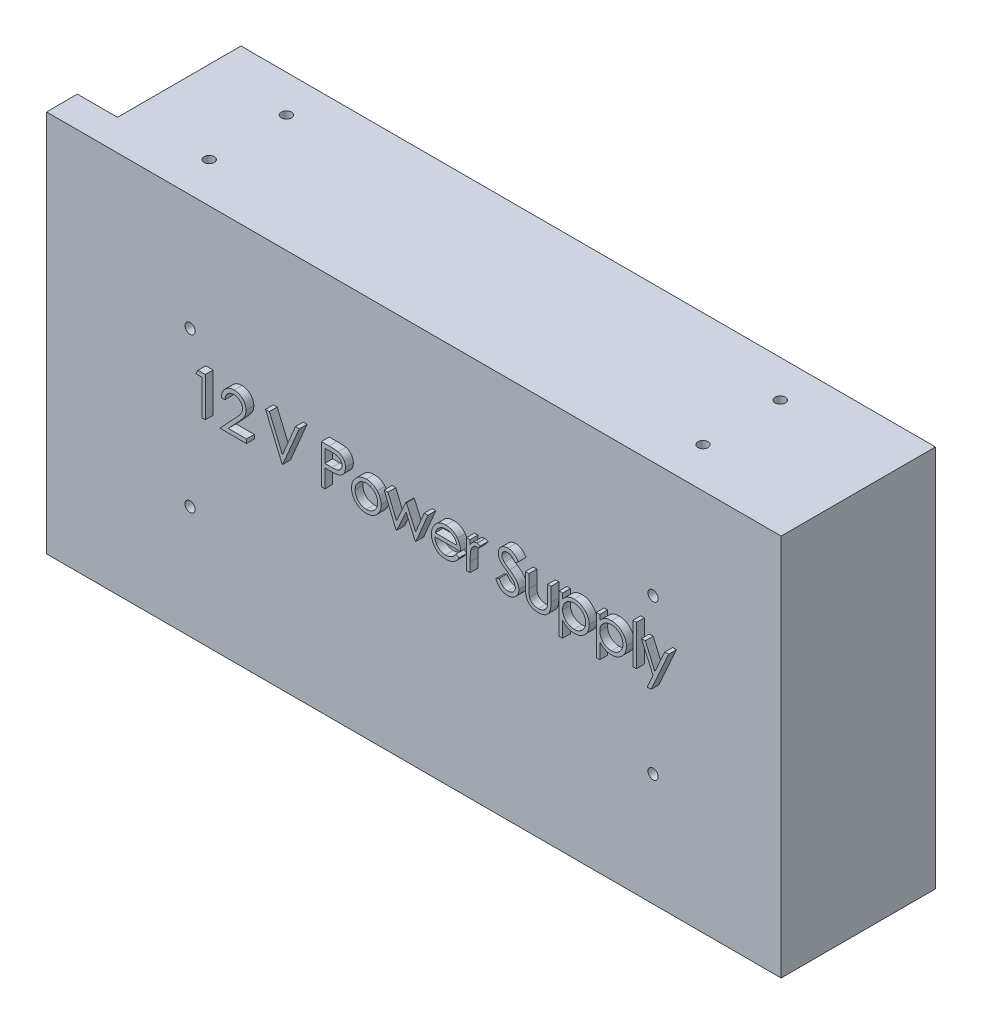
SolidWorks part; units mm, degrees
ref_plane "Front Plane" through (0, 0, 0) normal (0, 0, 1) x (1, 0, 0)
ref_plane "Top Plane" through (0, 0, 0) normal (0, 1, 0) x (1, 0, 0)
ref_plane "Right Plane" through (0, 0, 0) normal (1, 0, 0) x (0, 0, -1)
sketch "Sketch1" plane through (0, 0, 0) normal (0, 0, 1) x (1, 0, 0)
  line L1 (112.5, -62) -> (-112.5, -62)
  line L2 (112.5, -62) -> (112.5, 62)
  line L3 (112.5, 62) -> (-112.5, 62)
  line L4 (-112.5, -62) -> (-112.5, 62)
  line L5 (112.5, -62) -> (-112.5, 62) construction
  line L6 (112.5, 62) -> (-112.5, -62) construction
  point P0 (0, 0)
  dimension "D1" = 225
  dimension "D2" = 124
extrude "Boss-Extrude1" add sketch "Sketch1" along normal blind 50
sketch "Sketch2" plane through (0, 0, 50) normal (0, 0, 1) x (1, 0, 0)
  text T0 "12 V Power Supply" font "Century Gothic" height in points 48
extrude "Boss-Extrude2" add sketch "Sketch2" along normal blind 2.54
sketch "Sketch3" plane through (-112.5, 0, 0) normal (-1, 0, 0) x (0, 0, 1)
  line L0 (50, 62) -> (0, 62) construction
  line L1 (50, -62) -> (40, -62)
  line L2 (50, -62) -> (50, 62)
  line L3 (50, 62) -> (40, 62)
  line L4 (40, -62) -> (40, 62)
  dimension "D1" = 10
extrude "Boss-Extrude3" add sketch "Sketch3" along normal blind 13
hole_wizard "Tap Drill for M4x0.7 Tap1" positions "Sketch6" profile "Sketch7" hole size "M4x0.7" standard "ANSI Metric"
sketch "Sketch6" plane through (0, 0, 50) normal (0, 0, -1) x (-1, 0, 0)
  line L0 (-112.5, 62) -> (112.5, 62) construction
  line L2 (112.5, 62) -> (112.5, -62) construction
  point P0 (-71, 24.5)
  point P2 (79, 24.5)
  point P4 (79, -25.5)
  point P6 (-71, -25.5)
  dimension "D1" = 37.5
  dimension "D2" = 50
  dimension "D3" = 150
  dimension "D4" = 33.5
sketch "Sketch7" plane through (71, 24.5, 50) normal (1, 0, 0) x (0, -1, 0)
  line L0 (0, 0) -> (0, 5.9914)
  line L1 (0, 5.9914) -> (1.65, 5)
  line L2 (1.65, 5) -> (1.65, 0)
  line L5 (1.65, 0) -> (0, 0)
  line L10 (0, 5.9914) -> (-1.65, 5) construction
  line L11 (0, -6.35) -> (0, 107.95) construction
  dimension "Hole Dia." = 3.3
  dimension "Hole Depth" = 5
  dimension "Drill Angle" = 118
hole_wizard "Tap Drill for M4x0.7 Tap2" positions "Sketch8" profile "Sketch9" hole size "M4x0.7" standard "ANSI Metric"
sketch "Sketch8" plane through (0, 62, 0) normal (0, 1, 0) x (1, 0, 0)
  line L0 (-112.5, -40) -> (-112.5, 0) construction
  line L1 (112.5, -50) -> (-125.5, -50) construction
  point P0 (-85.8, -12)
  point P2 (-85.8, -37)
  point P4 (74.2, -37)
  point P6 (74.2, -12)
  point P15 (-112.5, -20)
  dimension "D1" = 26.7
  dimension "D2" = 160
  dimension "D3" = 25
  dimension "D4" = 13
sketch "Sketch9" plane through (-85.8, 62, 12) normal (1, 0, 0) x (0, 0, 1)
  line L0 (0, 0) -> (0, 3.9914)
  line L1 (0, 3.9914) -> (1.65, 3)
  line L2 (1.65, 3) -> (1.65, 0)
  line L5 (1.65, 0) -> (0, 0)
  line L10 (0, 3.9914) -> (-1.65, 3) construction
  line L11 (0, -6.35) -> (0, 107.95) construction
  dimension "Hole Dia." = 3.3
  dimension "Hole Depth" = 3
  dimension "Drill Angle" = 118
mirror "Mirror1" about plane through (0, 0, 0) normal (0, 1, 0) of "Tap Drill for M4x0.7 Tap2"
sketch "Sketch10" plane through (0, 0, 0) normal (0, 0, -1) x (-1, 0, 0)
  text T0 "FAN SIDE" font "Century Gothic" height 10
extrude "Boss-Extrude4" add sketch "Sketch10" along normal blind 1
